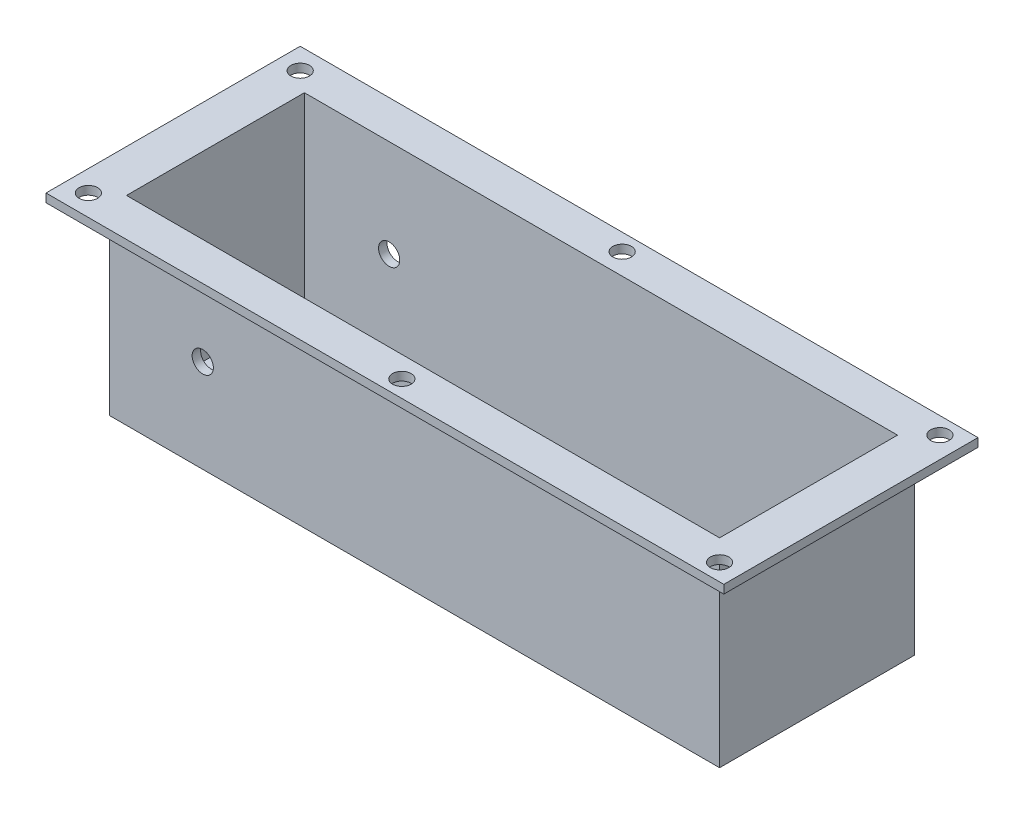
SolidWorks part; units mm, degrees
ref_plane "Front Plane" through (0, 0, 0) normal (0, 0, 1) x (1, 0, 0)
ref_plane "Top Plane" through (0, 0, 0) normal (0, 1, 0) x (1, 0, 0)
ref_plane "Right Plane" through (0, 0, 0) normal (1, 0, 0) x (0, 0, -1)
sketch "Sketch3" plane through (0, 0, 0) normal (0, 1, 0) x (1, 0, 0)
  line L1 (-91.44, 29.21) -> (91.44, 29.21)
  line L2 (-91.44, 29.21) -> (-91.44, -29.21)
  line L3 (-91.44, -29.21) -> (91.44, -29.21)
  line L4 (91.44, 29.21) -> (91.44, -29.21)
  line L5 (-91.44, 29.21) -> (91.44, -29.21) construction
  line L6 (-91.44, -29.21) -> (91.44, 29.21) construction
  point P0 (0, 0)
  dimension "D1" = 58.42
  dimension "D2" = 182.88
extrude "Boss-Extrude1" add sketch "Sketch3" against normal blind 57.15
sketch "Sketch4" plane through (0, 0, 0) normal (0, 1, 0) x (1, 0, 0)
  line L1 (-101.6, -38.1) -> (101.6, -38.1)
  line L2 (-101.6, -38.1) -> (-101.6, 38.1)
  line L3 (-101.6, 38.1) -> (101.6, 38.1)
  line L4 (101.6, -38.1) -> (101.6, 38.1)
  line L5 (-101.6, -38.1) -> (101.6, 38.1) construction
  line L6 (-101.6, 38.1) -> (101.6, -38.1) construction
  point P0 (0, 0)
  dimension "D1" = 76.2
  dimension "D2" = 203.2
extrude "Boss-Extrude2" add sketch "Sketch4" against normal blind 2.54
sketch "Sketch5" plane through (0, 0, 0) normal (0, 1, 0) x (1, 0, 0)
  line L1 (-88.9, -26.67) -> (88.9, -26.67)
  line L2 (-88.9, -26.67) -> (-88.9, 26.67)
  line L3 (-88.9, 26.67) -> (88.9, 26.67)
  line L4 (88.9, -26.67) -> (88.9, 26.67)
  line L5 (-88.9, -26.67) -> (88.9, 26.67) construction
  line L6 (-88.9, 26.67) -> (88.9, -26.67) construction
  point P0 (0, 0)
  dimension "D1" = 53.34
  dimension "D2" = 177.8
extrude "Cut-Extrude1" cut sketch "Sketch5" against normal blind 54.61
sketch "Sketch6" plane through (0, 0, 0) normal (0, 1, 0) x (1, 0, 0)
  line L0 (88.9, 26.67) -> (-88.9, 26.67) construction
  line L1 (-88.9, 26.67) -> (-88.9, -26.67) construction
  line L2 (88.9, -26.67) -> (88.9, 26.67) construction
  line L3 (-118.5656, 0) -> (108.8741, 0) construction
  circle A0 centre (-95.25, 31.75) radius 2.7813
  circle A1 centre (0, 33.02) radius 2.7813
  circle A2 centre (95.25, 33.02) radius 2.7813
  circle A3 centre (95.25, -33.02) radius 2.7813
  circle A4 centre (0, -33.02) radius 2.7813
  circle A5 centre (-95.25, -31.75) radius 2.7813
  dimension "D1" = 5.5626
  dimension "D4" = 5.5626
  dimension "D6" = 5.5626
  dimension "D2" = 5.08
  dimension "D3" = 6.35
  dimension "D5" = 6.35
  dimension "D7" = 6.35
  dimension "D8" = 6.35
extrude "Cut-Extrude2" cut sketch "Sketch6" against normal blind 53.34
sketch "Sketch8" plane through (0, 0, 0) normal (0, 0, 1) x (1, 0, 0)
  line L0 (-91.44, -57.15) -> (91.44, -57.15) construction
  line L1 (-91.44, -57.15) -> (-91.44, -2.54) construction
  circle A0 centre (-63.5, -29.21) radius 3.1813
  dimension "D1" = 6.3627
  dimension "D2" = 27.94
  dimension "D3" = 27.94
extrude "Cut-Extrude3" cut sketch "Sketch8" against normal mid plane 76.2
